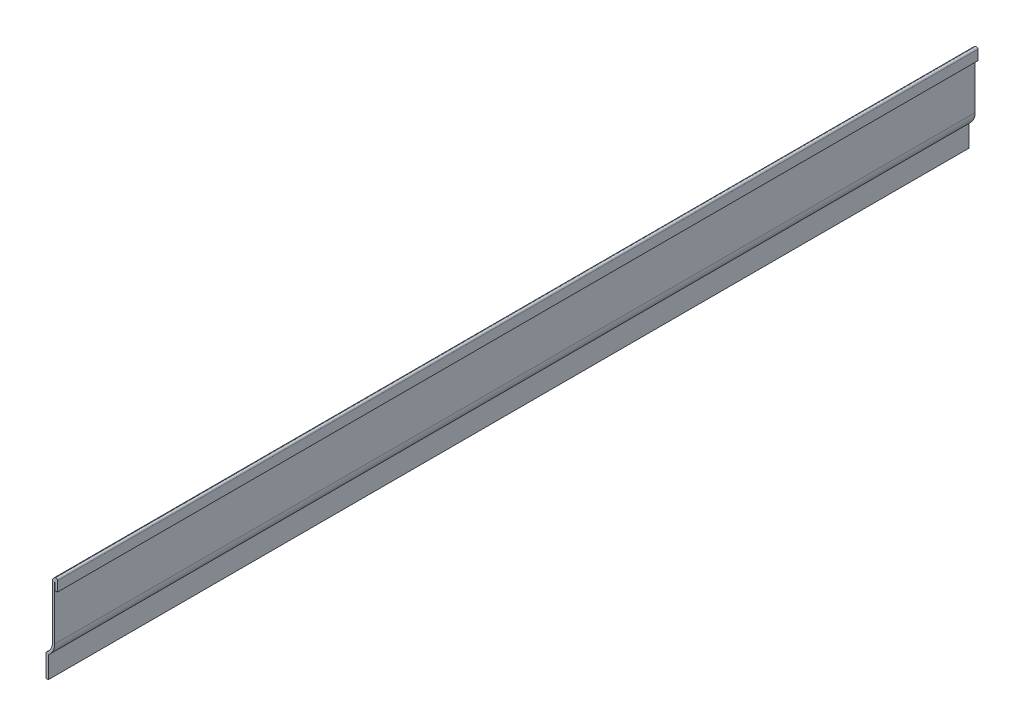
SolidWorks part; units mm, degrees
ref_plane "Front Plane" through (0, 0, 0) normal (0, 0, 1) x (1, 0, 0)
ref_plane "Top Plane" through (0, 0, 0) normal (0, 1, 0) x (1, 0, 0)
ref_plane "Right Plane" through (0, 0, 0) normal (1, 0, 0) x (0, 0, -1)
sketch "Sketch1" plane through (0, 0, 0) normal (0, 0, 1) x (1, 0, 0)
  line L0 (0, 44.45) -> (0, 50.8)
  line L1 (-2.794, 48.4548) -> (-2.794, 18.8775)
  line L2 (-6.35, 12.7) -> (-6.35, 0)
  line L3 (-6.35, 0) -> (0, 0) construction
  line L4 (0, 0) -> (0, 44.45) construction
  arc A0 (-2.794, 48.4548) -> (0, 50.8) centre (-0.4128, 48.4548) cw
  arc A1 (-2.794, 18.8775) -> (-6.35, 12.7) centre (-9.9377, 18.8775) cw
  point P9 (0, 0)
  point P10 (0, 0)
  point P12 (-3.8804, 48.9499)
  dimension "D2" = 2.3813
  dimension "D5" = 7.1437
  dimension "D1" = 6.35
  dimension "D3" = 38.1
  dimension "D4" = 12.7
  dimension "D6" = 6.35
  dimension "D7" = 2.794
extrude "Extrude-Thin1" add sketch "Sketch1" against normal blind 508 thin contours L0 A0 L1 A1 L2 thin type one direction reverse wall 1.27
fillet "Fillet1" radius 1.27 1 edges at (-6.35, 12.7, -254)
fillet "Fillet2" radius 0.889 1 edges at (0, 50.8, -254)
